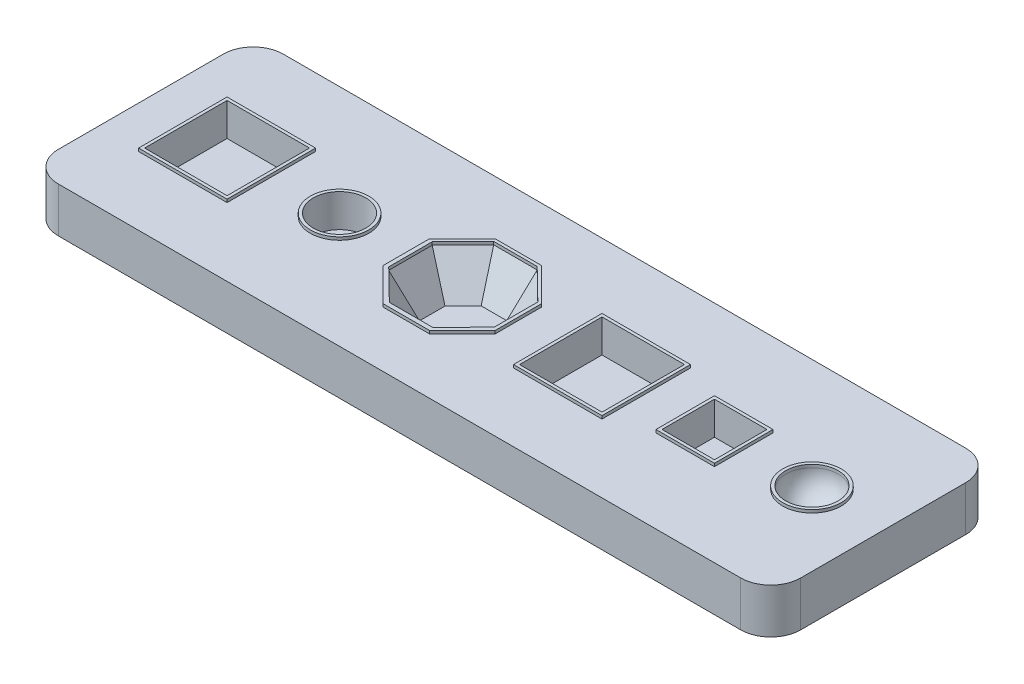
SolidWorks part; units mm, degrees
material "Maple"
ref_plane "Front Plane" through (0, 0, 0) normal (0, 0, 1) x (1, 0, 0)
ref_plane "Top Plane" through (0, 0, 0) normal (0, 1, 0) x (1, 0, 0)
ref_plane "Right Plane" through (0, 0, 0) normal (1, 0, 0) x (0, 0, -1)
sketch "Sketch1" plane through (0, 0, 0) normal (0, 1, 0) x (1, 0, 0)
  line L1 (-247.5, -75) -> (247.5, -75)
  line L2 (-247.5, -75) -> (-247.5, 75)
  line L3 (-247.5, 75) -> (247.5, 75)
  line L4 (247.5, -75) -> (247.5, 75)
  line L5 (-247.5, -75) -> (247.5, 75) construction
  line L6 (-247.5, 75) -> (247.5, -75) construction
  point P0 (0, 0)
  dimension "D1" = 495
  dimension "D2" = 150
extrude "Boss-Extrude1" add sketch "Sketch1" along normal blind 30
sketch "Sketch2" plane through (0, 30, 0) normal (0, 1, 0) x (1, 0, 0)
  line L0 (-247.5, 75) -> (-247.5, -75) construction
  line L1 (-217.5, 27.5) -> (-162.5, 27.5)
  line L2 (-217.5, 27.5) -> (-217.5, -27.5)
  line L3 (-217.5, -27.5) -> (-162.5, -27.5)
  line L4 (-162.5, 27.5) -> (-162.5, -27.5)
  line L5 (247.5, 75) -> (-247.5, 75) construction
  line L7 (-55, 0) -> (55, 0) construction
  circle A0 centre (-115, 0) radius 17.5
  dimension "D5" = 47.5
  dimension "D6" = 35
  dimension "D1" = 30
  dimension "D2" = 55
  dimension "D3" = 55
  dimension "D4" = 47.5
sketch "Sketch4" plane through (0, 30, 0) normal (0, 1, 0) x (1, 0, 0)
  line L0 (-67.5, 14.2879) -> (-67.5, -14.7121)
  line L1 (-18.2071, 35.005) -> (-47.2071, 35.005)
  line L2 (-47.2071, 35.005) -> (-67.5, 14.2879)
  line L3 (-67.5, -14.7121) -> (-46.7829, -35.005)
  line L4 (-46.7829, -35.005) -> (-17.7829, -35.005)
  line L5 (-17.7829, -35.005) -> (2.51, -14.2879)
  line L6 (2.51, -14.2879) -> (2.51, 14.7121)
  line L7 (2.51, 14.7121) -> (-18.2071, 35.005)
  line L8 (247.5, 75) -> (-247.5, 75) construction
  line L9 (-247.5, -75) -> (247.5, -75) construction
  circle A0 centre (-115, 0) radius 17.5 construction
  dimension "D9" = 47.5
  dimension "D1" = 29
  dimension "D2" = 29
  dimension "D3" = 29
  dimension "D4" = 29
  dimension "D5" = 29
  dimension "D6" = 29
  dimension "D7" = 39.995
  dimension "D8" = 39.995
sketch "Sketch5" plane through (0, 30, 0) normal (0, 1, 0) x (1, 0, 0)
  line L0 (-55, 0) -> (55, 0) construction
  line L1 (32.51, -27.5) -> (87.51, -27.5)
  line L2 (32.51, -27.5) -> (32.51, 27.5)
  line L3 (32.51, 27.5) -> (87.51, 27.5)
  line L4 (87.51, -27.5) -> (87.51, 27.5)
  line L5 (32.51, -27.5) -> (87.51, 27.5) construction
  line L6 (32.51, 27.5) -> (87.51, -27.5) construction
  line L8 (2.51, -14.2879) -> (2.51, 14.7121) construction
  line L10 (117.51, -17.5) -> (152.51, -17.5)
  line L11 (117.51, -17.5) -> (117.51, 17.5)
  line L12 (117.51, 17.5) -> (152.51, 17.5)
  line L13 (152.51, -17.5) -> (152.51, 17.5)
  line L14 (117.51, -17.5) -> (152.51, 17.5) construction
  line L15 (117.51, 17.5) -> (152.51, -17.5) construction
  point P0 (60.01, 0)
  point P9 (135.01, 0)
  dimension "D1" = 55
  dimension "D2" = 55
  dimension "D3" = 30
  dimension "D4" = 35
  dimension "D5" = 35
  dimension "D6" = 30
sketch "Sketch6" plane through (0, 30, 0) normal (0, 1, 0) x (1, 0, 0)
  line L0 (-55, 0) -> (55, 0) construction
  line L1 (217.51, 0) -> (182.51, 0)
  line L2 (152.51, -17.5) -> (152.51, 17.5) construction
  arc A0 (217.51, 0) -> (182.51, 0) centre (200.01, 0) ccw
  dimension "D1" = 35
  dimension "D2" = 47.5
extrude "Cut-Extrude1" cut sketch "Sketch2" against normal blind 20
extrude "Cut-Extrude2" cut sketch "Sketch4" against normal blind 25 draft 30
extrude "Cut-Extrude3" cut sketch "Sketch5" against normal blind 20
revolve "Cut-Revolve1" cut sketch "Sketch6" angle 360 about L1
fillet "Fillet1" radius 20 4 edges at (-247.5, 15, -75) (247.5, 15, -75) (247.5, 15, 75) (-247.5, 15, 75)
sketch "Sketch8" plane through (0, 30, 0) normal (0, 1, 0) x (1, 0, 0)
  line L0 (-16.5, 0) -> (16.5, 0) construction
  line L1 (-219.5, -29.5) -> (-160.5, -29.5)
  line L2 (-219.5, -29.5) -> (-219.5, 29.5)
  line L3 (-219.5, 29.5) -> (-160.5, 29.5)
  line L4 (-160.5, -29.5) -> (-160.5, 29.5)
  line L5 (-219.5, -29.5) -> (-160.5, 29.5) construction
  line L6 (-219.5, 29.5) -> (-160.5, -29.5) construction
  line L7 (-217.5, 27.5) -> (-217.5, -27.5) construction
  line L8 (-162.5, -27.5) -> (-162.5, 27.5) construction
  line L9 (-162.5, 27.5) -> (-217.5, 27.5) construction
  line L10 (-217.5, 27.5) -> (-217.5, -27.5)
  line L11 (-217.5, -27.5) -> (-162.5, -27.5)
  line L12 (-162.5, -27.5) -> (-162.5, 27.5)
  line L13 (-162.5, 27.5) -> (-217.5, 27.5)
  point P0 (-190, 0)
  dimension "D1" = 2
  dimension "D2" = 2
  dimension "D3" = 2
extrude "Boss-Extrude2" add sketch "Sketch8" along normal blind 2
sketch "Sketch9" plane through (0, 30, 0) normal (0, 1, 0) x (1, 0, 0)
  circle A3 centre (-115, 0) radius 19.5
  circle A4 centre (-115, 0) radius 17.5
  dimension "D1" = 39
extrude "Boss-Extrude3" add sketch "Sketch9" along normal blind 2
sketch "Sketch10" plane through (0, 30, 0) normal (0, 1, 0) x (1, 0, 0)
  line L0 (-47.2071, 35.005) -> (-18.2071, 35.005)
  line L1 (-18.2071, 35.005) -> (2.51, 14.7121)
  line L2 (2.51, 14.7121) -> (2.51, -14.2879)
  line L3 (2.51, -14.2879) -> (-17.7829, -35.005)
  line L4 (-17.7829, -35.005) -> (-46.7829, -35.005)
  line L5 (-46.7829, -35.005) -> (-67.5, -14.7121)
  line L6 (-67.5, -14.7121) -> (-67.5, 14.2879)
  line L7 (-67.5, 14.2879) -> (-47.2071, 35.005)
  line L8 (-48.2071, 37.005) -> (-17.2071, 37.005)
  line L9 (-70.1274, 15.0847) -> (-70.1274, -15.9153)
  line L10 (-70.1274, -15.9153) -> (-48.2071, -37.8356)
  line L11 (-48.2071, 37.005) -> (-70.1274, 15.0847)
  line L12 (-48.2071, -37.8356) -> (-17.2071, -37.8356)
  line L13 (-17.2071, -37.8356) -> (4.7132, -15.9153)
  line L14 (4.7132, -15.9153) -> (4.7132, 15.0847)
  line L15 (4.7132, 15.0847) -> (-17.2071, 37.005)
  dimension "D1" = 31
  dimension "D2" = 2
  dimension "D3" = 31
  dimension "D4" = 31
extrude "Boss-Extrude4" add sketch "Sketch10" along normal blind 2
sketch "Sketch11" plane through (0, 30, 0) normal (0, 1, 0) x (1, 0, 0)
  line L3 (87.51, 27.5) -> (32.51, 27.5) construction
  line L4 (30.51, -29.5) -> (89.51, -29.5)
  line L5 (30.51, -29.5) -> (30.51, 29.5)
  line L6 (30.51, 29.5) -> (89.51, 29.5)
  line L7 (89.51, -29.5) -> (89.51, 29.5)
  line L8 (30.51, -29.5) -> (89.51, 29.5) construction
  line L9 (30.51, 29.5) -> (89.51, -29.5) construction
  line L10 (32.51, 27.5) -> (32.51, -27.5) construction
  line L11 (32.51, 27.5) -> (87.51, 27.5)
  line L12 (32.51, 27.5) -> (32.51, -27.5)
  line L13 (32.51, -27.5) -> (87.51, -27.5)
  line L14 (87.51, 27.5) -> (87.51, -27.5)
  dimension "D2" = 2
  dimension "D3" = 2
extrude "Boss-Extrude6" add sketch "Sketch11" along normal blind 2
sketch "Sketch12" plane through (0, 30, 0) normal (0, 1, 0) x (1, 0, 0)
  line L1 (117.51, 17.5) -> (152.51, 17.5)
  line L2 (117.51, 17.5) -> (117.51, -17.5)
  line L3 (117.51, -17.5) -> (152.51, -17.5)
  line L4 (152.51, 17.5) -> (152.51, -17.5)
  line L5 (115.51, -19.5) -> (154.51, -19.5)
  line L6 (115.51, -19.5) -> (115.51, 19.5)
  line L7 (115.51, 19.5) -> (154.51, 19.5)
  line L8 (154.51, -19.5) -> (154.51, 19.5)
  line L9 (115.51, -19.5) -> (154.51, 19.5) construction
  line L10 (115.51, 19.5) -> (154.51, -19.5) construction
  point P6 (135.01, 0)
  dimension "D1" = 2
  dimension "D2" = 2
  dimension "D3" = 2
  dimension "D4" = 2
extrude "Boss-Extrude7" add sketch "Sketch12" along normal blind 2
sketch "Sketch13" plane through (0, 30, 0) normal (0, 1, 0) x (1, 0, 0)
  line L1 (-17.6, 0) -> (17.6, 0) construction
  circle A1 centre (200.01, 0) radius 17.5
  circle A2 centre (200.01, 0) radius 19.5
  dimension "D1" = 39
  dimension "D2" = 35
extrude "Boss-Extrude8" add sketch "Sketch13" along normal blind 2
